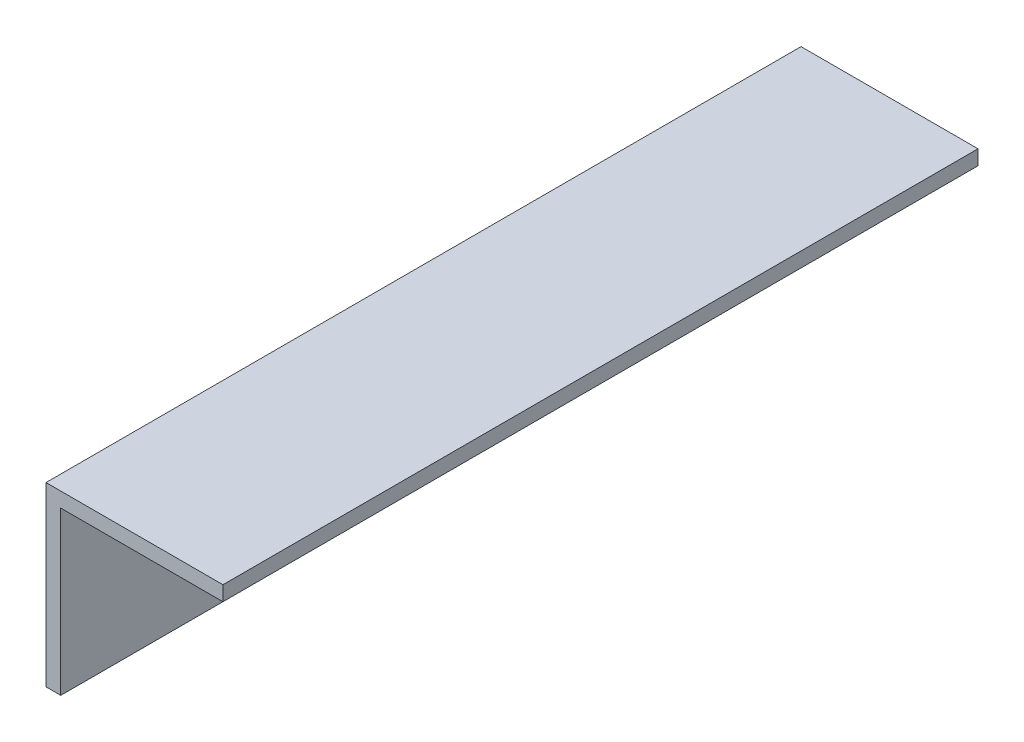
SolidWorks part; units mm, degrees
material "6061-T6 (SS)"
ref_plane "Front Plane" through (0, 0, 0) normal (0, 0, 1) x (1, 0, 0)
ref_plane "Top Plane" through (0, 0, 0) normal (0, 1, 0) x (1, 0, 0)
ref_plane "Right Plane" through (0, 0, 0) normal (1, 0, 0) x (0, 0, -1)
sketch "Sketch1" plane through (0, 0, 0) normal (0, 0, 1) x (1, 0, 0)
  line L0 (0, 0) -> (0, 19.05)
  line L1 (0, 19.05) -> (19.05, 19.05)
  line L2 (19.05, 19.05) -> (19.05, 17.4625)
  line L3 (19.05, 17.4625) -> (1.5875, 17.4625)
  line L4 (1.5875, 17.4625) -> (1.5875, 0)
  line L5 (1.5875, 0) -> (0, 0)
  dimension "D1" = 19.05
  dimension "D2" = 1.5875
extrude "Boss-Extrude1" add sketch "Sketch1" along normal blind 81.28
